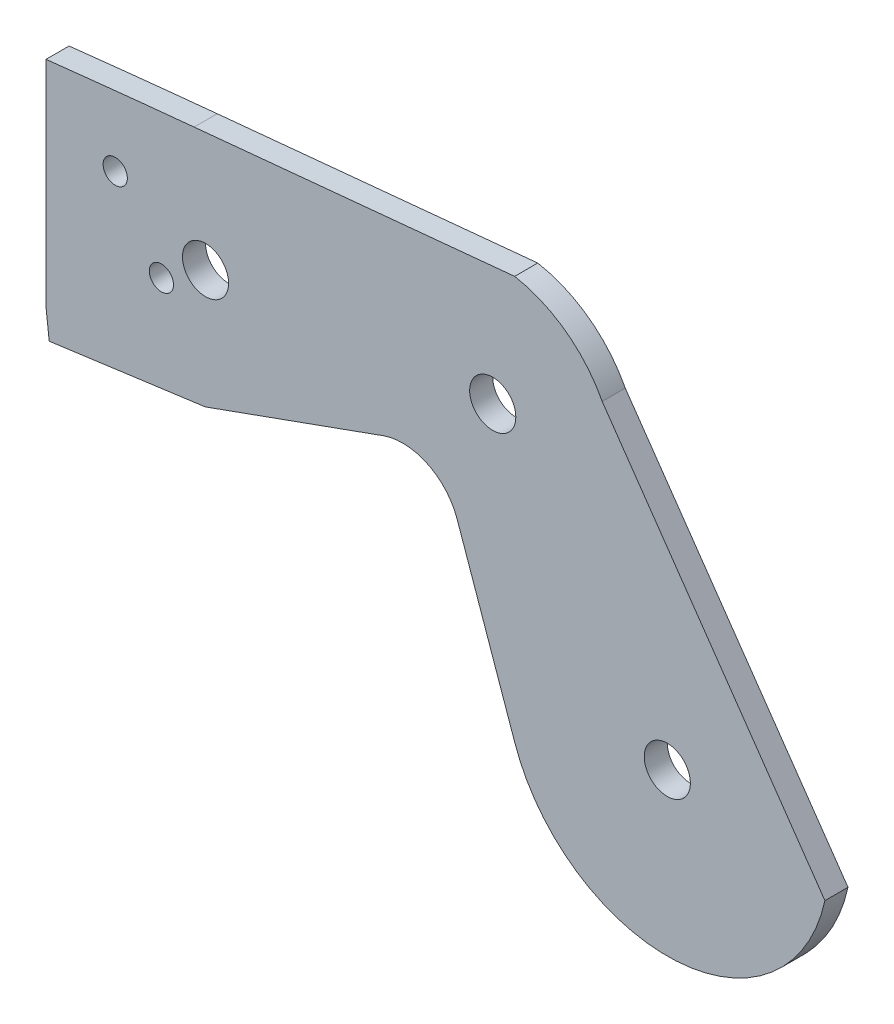
SolidWorks part; units mm, degrees
ref_plane "前视基准面" through (0, 0, 0) normal (0, 0, 1) x (1, 0, 0)
ref_plane "上视基准面" through (0, 0, 0) normal (0, 1, 0) x (1, 0, 0)
ref_plane "右视基准面" through (0, 0, 0) normal (1, 0, 0) x (0, 0, -1)
sketch "草图1" plane through (0, 0, 0) normal (0, 0, 1) x (1, 0, 0)
  line L0 (27.6443, 65) -> (77.4123, 69.8109)
  line L1 (77.4123, 69.8109) -> (107.6628, 30)
  line L2 (107.6628, 30) -> (27.6443, 65)
  line L3 (0, 0) -> (0, 252.2874)
  line L4 (0, 0) -> (398.1835, 0)
  line L5 (0, 0) -> (50, 0)
  line L6 (50, 0) -> (50, -60.1662)
  line L7 (25.6658, 85.4679) -> (81.2137, 90.8376)
  line L8 (96.3803, 79.649) -> (134.9771, 24.0341)
  line L9 (27.5954, 44.4367) -> (58.4244, 55.5258)
  line L10 (71.2478, 49.4192) -> (81.1758, 21.0504)
  line L11 (-4.1697, 82.3303) -> (0.5545, 40.773)
  line L12 (0.5545, 40.773) -> (27.5954, 44.4367)
  circle A0 centre (107.6628, 30) radius 4
  circle A1 centre (77.4123, 69.8109) radius 4
  circle A2 centre (27.6443, 65) radius 4
  arc A3 (25.6658, 85.4679) -> (27.5954, 44.4367) centre (27.6443, 65) ccw
  arc A4 (96.3803, 79.649) -> (81.2137, 90.8376) centre (77.4123, 69.8109) ccw
  arc A5 (81.1758, 21.0504) -> (134.9771, 24.0341) centre (107.6628, 30) ccw
  arc A6 (58.4244, 55.5258) -> (71.2478, 49.4192) centre (61.8091, 46.116) cw
  arc A7 (25.6658, 85.4679) -> (-4.1697, 82.3303) centre (197.2209, -1689.238) ccw
  circle A8 centre (20, 60) radius 2.1
  circle A9 centre (12, 72) radius 2.1
  point P2 (0, 0)
  point P29 (0, 0)
  dimension "D2" = 50
  dimension "D7" = 10
  dimension "D8" = 30
  dimension "D9" = 60
  dimension "D15" = 8
  dimension "D1" = 30
  dimension "D3" = 50
  dimension "D4" = 50
  dimension "D5" = 65
  dimension "D6" = 65
  dimension "D10" = 30
  dimension "D11" = 38
  dimension "D12" = 72
  dimension "D13" = 75
  dimension "D14" = 22.3557
extrude "凸台-拉伸1" add sketch "草图1" along normal blind 4 contours L10 A5 L8 A4 L7 A3 L9 L2 A2 L0 A1 L1 A0 | L9 A6 L10 L2 A0 L1 A1 L0 A2 | A3 A7 L11 L12 A9
